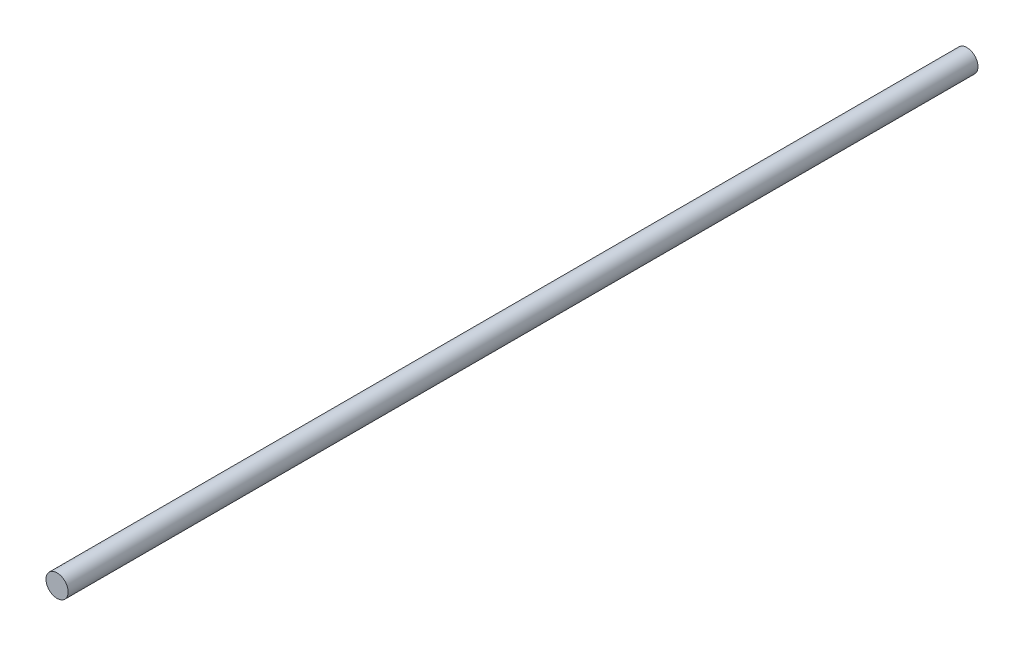
SolidWorks part; units mm, degrees
material "AISI 1010 Steel, hot rolled bar"
ref_plane "Front Plane" through (0, 0, 0) normal (0, 0, 1) x (1, 0, 0)
ref_plane "Top Plane" through (0, 0, 0) normal (0, 1, 0) x (1, 0, 0)
ref_plane "Right Plane" through (0, 0, 0) normal (1, 0, 0) x (0, 0, -1)
sketch "Sketch1" plane through (0, 0, 0) normal (0, 0, 1) x (1, 0, 0)
  circle A0 centre (0, 0) radius 5
  dimension "D1" = 10
extrude "Boss-Extrude1" add sketch "Sketch1" along normal mid plane 410
